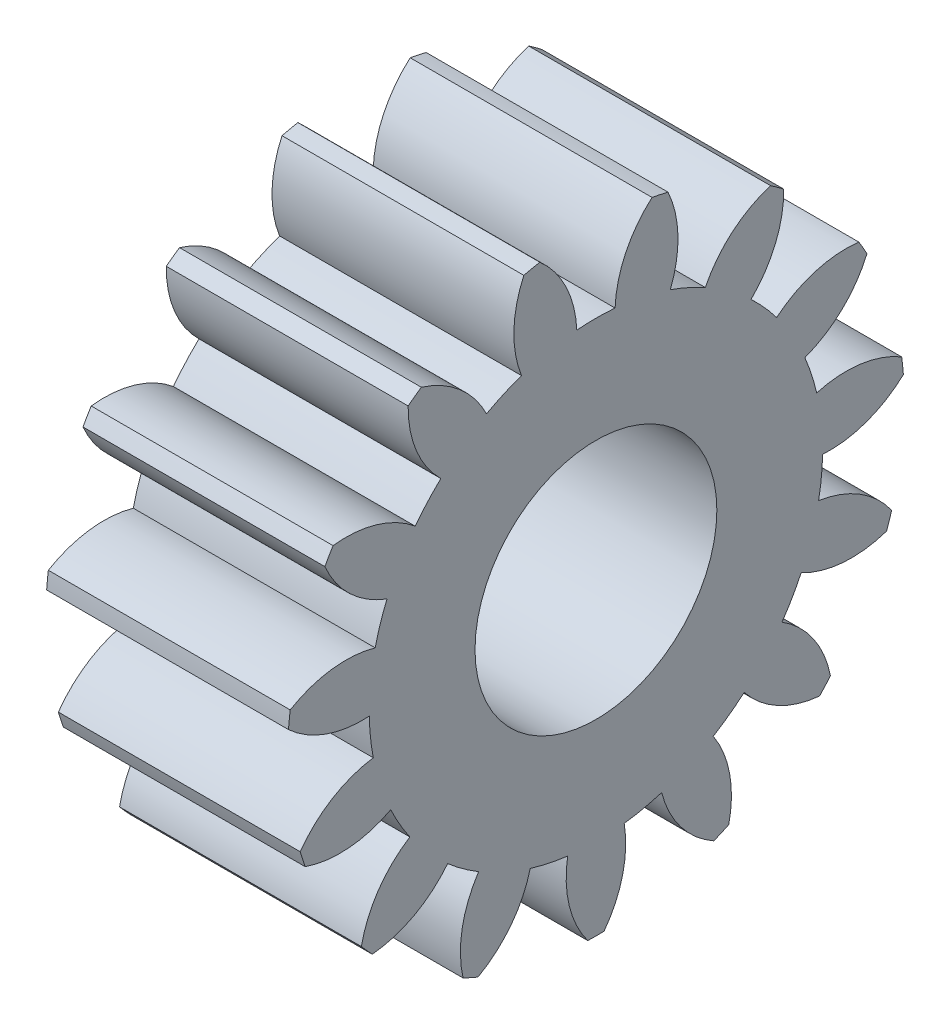
SolidWorks part; units mm, degrees
ref_plane "Plane1" through (0, 0, 0) normal (0, 0, 1) x (1, 0, 0)
ref_plane "Plane2" through (0, 0, 0) normal (0, 1, 0) x (1, 0, 0)
ref_plane "Plane3" through (0, 0, 0) normal (1, 0, 0) x (0, 0, -1)
other "Configuration Table"
sketch "HoldingSke" plane through (0, 0, 0) normal (0, 1, 0) x (1, 0, 0)
  line L0 (0, 0) -> (0.644, -0.1725)
  line L1 (-15, 0) -> (100, 0) construction
  line L2 (0, 0) -> (-2.1039, 2.3779)
  line L3 (0, 0) -> (-11.863, 4.5341)
  line L4 (0, 0) -> (8.3417, 2.2352)
  line L5 (0, 0) -> (-46.8476, -17.4728)
  line L6 (0, 0) -> (-8.2896, -5.593)
  line L7 (-2.1039, 2.3779) -> (8.6586, 51.2059)
  line L8 (-76.2, 54.61) -> (-74.4, 54.61)
  line L9 (-71.009, 38.7566) -> (-53.1078, 45.2721)
  line L10 (-76.2, 71.12) -> (104.1128, 71.12)
  line L11 (0, 0) -> (-10, 0)
  line L12 (-76.2, 101.6) -> (-76.147, 101.6)
  line L13 (24.9733, 27.94) -> (52.9518, 28.4284)
  line L14 (24.9733, 27.94) -> (24.9743, 27.94)
  line L15 (24.9733, 27.94) -> (100.4006, 29.5858)
  line L16 (-63.627, -1.5) -> (-12.827, -1.5)
  circle A0 centre (0, 0) radius 5
  circle A1 centre (0, 0) radius 9.374
  circle A2 centre (0, 0) radius 37.5
  circle A3 centre (0, 0) radius 5
  dimension "MHD" = 18.748
  dimension "Hub_dia" = 75
  dimension "Bore" = 10
  dimension "MBD" = 10
  dimension "Num_teeth" = 15
  dimension "Pitch" = 0.6667
  dimension "Overall_len" = 50
  dimension "Show_teeth" = 15
  dimension "Thickness" = 10
  dimension "OAL" = 50.0001
  dimension "T_dim" = 1.8
  dimension "Ap" = 20
  dimension "H" = 19.05
  dimension "Pitch_radius" = 180.3128
  dimension "Width" = 10
  dimension "Backlash" = 0.053
  dimension "Addendum_fac" = 1
  dimension "Dedendum_fac" = 1.25
  dimension "Clearance_fac" = 0.25
  dimension "Dedendum_add" = 0.001
  dimension "Module" = 1.5
sketch "BasProSke" plane through (0, 0, 0) normal (0, 1, 0) x (1, 0, 0)
  line L0 (-10, 0) -> (60, 0) construction
  line L1 (0, 0) -> (0, 12.75)
  line L2 (0, 0) -> (10, 0)
  line L3 (10, 0) -> (10, 12.75)
  line L4 (10, 12.75) -> (0, 12.75)
  dimension "Thickness" = 10
  dimension "Diameter" = 25.5
revolve "Base-Revolve" add sketch "BasProSke" angle 360 about L0
sketch "TooCutSke" plane through (0, 0, 0) normal (1, 0, 0) x (0, 0, -1)
  line L1 (0, 0) -> (0, 107) construction
  line L2 (0, 0) -> (-1.2686, 11.1782) construction
  line L3 (0, 0) -> (-4.6563, 21.9061) construction
  line L4 (-1.2686, 11.1782) -> (-2.3281, 10.953) construction
  arc A0 (0.7915, 9.3405) -> (-0.7915, 9.3405) centre (0, 0) ccw
  arc A1 (2.3447, 12.5584) -> (-2.3447, 12.5584) centre (0, 0) ccw
  circle A2 centre (0, 0) radius 11.25 construction
  circle A3 centre (0, 0) radius 10.5715 construction
  arc A4 (-0.7915, 9.3405) -> (-2.3447, 12.5584) centre (-5.2877, 9.1541) ccw
  arc A5 (2.3447, 12.5584) -> (0.7915, 9.3405) centre (5.2877, 9.1541) ccw
  dimension "Root_dia" = 18.748
  dimension "Overcut_dia" = 25.5508
  dimension "Pitch_dia" = 22.5
  dimension "Base_dia" = 21.1431
  dimension "Flank_rad" = 4.5
  dimension "Half_ang" = 12
  dimension "Half_CT" = 1.0832
extrude "ToothCut" cut sketch "TooCutSke" along normal through all
fillet "Breaks" [suppressed] radius 0.03
fillet "RootFillets" [suppressed] radius 0.376
pattern_circular "TeethCuts" count 15 every 24 about axis through (-10, 0, 0) along (1, 0, 0) of "ToothCut", "RootFillets", "Breaks"
sketch "HubNeaOneSke" plane through (0, 0, 0) normal (-1, 0, 0) x (0, 0, 1)
  circle A0 centre (0, 0) radius 9.374
  dimension "Diameter" = 18.748
extrude "HubNearOne" [suppressed] add sketch "HubNeaOneSke" along normal blind 40.0001
sketch "HubNeaBotSke" plane through (0, 0, 0) normal (-1, 0, 0) x (0, 0, 1)
  circle A0 centre (0, 0) radius 9.374
  dimension "Diameter" = 18.748
extrude "HubNearBoth" [suppressed] add sketch "HubNeaBotSke" along normal blind 20
ref_plane "FarPln" through (10, 0, 0) normal (1, 0, 0) x (0, 0, -1)
sketch "HubFarSke" plane through (10, 0, 0) normal (1, 0, 0) x (0, 0, -1)
  circle A0 centre (0, 0) radius 9.374
  dimension "Diameter" = 18.748
extrude "HubFar" [suppressed] add sketch "HubFarSke" along normal blind 20
sketch "BorSke" plane through (0, 0, 0) normal (1, 0, 0) x (0, 0, -1)
  circle A0 centre (0, 0) radius 5
  dimension "Diameter" = 10
extrude "Bore" cut sketch "BorSke" along normal mid plane 100.0001
sketch "KeySke" plane through (0, 0, 0) normal (1, 0, 0) x (0, 0, -1)
  line L0 (-2, 0) -> (-2, 6.8)
  line L1 (-2, 6.8) -> (2, 6.8)
  line L2 (2, 6.8) -> (2, 0)
  line L3 (0, 0) -> (0, 34) construction
  line L4 (-2, 0) -> (2, 0)
  dimension "Offset" = 6.8
  dimension "Width" = 4
extrude "Keyway" [suppressed] cut sketch "KeySke" along normal mid plane 100.0001
pattern_circular "Keyway2" [suppressed] count 2 every 90 about axis through (-10, 0, 0) along (1, 0, 0)
equation "' \"Module@HoldingSke\" = 6.35"
equation "' \"Num_teeth@HoldingSke\" = 12"
equation "' \"Ap@HoldingSke\" =  20"
equation "' \"Ap@HoldingSke\" = 20"
equation "' \"Width@HoldingSke\" = 0.5 * 25.4"
equation "' \"Hub_dia@HoldingSke\"= 1 * 25.4"
equation "' \"Hub_dia@HoldingSke\" = 1 * 25.4"
equation "' \"Overall_len@HoldingSke\" = 1.0 * 25.4"
equation "' \"Bore@HoldingSke\" = 0.75 * 25.4"
equation "' \"T_dim@HoldingSke\" = 0.1 * 25.4"
equation "' \"Width@KeySke\" = 0.25 * 25.4"
equation "' \"Show_teeth@HoldingSke\" = 13"
equation "' \"Backlash@HoldingSke\" = 0.009 * 25.4"
equation "' \"Addendum_fac@HoldingSke\" = 1.0"
equation "' \"Dedendum_fac@HoldingSke\" = 1.25"
equation "' \"Dedendum_add@HoldingSke\" = 0.00005 * 25.4"
equation "' \"Clearance_fac@HoldingSke\" = 0.25"
equation "\"Pitch@HoldingSke\" = 1 / \"Module@HoldingSke\""
equation "\"Overcut_dia@TooCutSke\" = (\"Num_teeth@HoldingSke\" + 2 * \"Addendum_fac@HoldingSke\") / \"Pitch@HoldingSke\" + 0.002 * 25.4"
equation "\"Pitch_dia@TooCutSke\" = \"Num_teeth@HoldingSke\" / \"Pitch@HoldingSke\""
equation "\"Base_dia@TooCutSke\" = \"Num_teeth@HoldingSke\" / \"Pitch@HoldingSke\" * cos((\"Ap@HoldingSke\"  * 3.14159265 / 180))"
equation "\"Root_dia@TooCutSke\" = (\"Num_teeth@HoldingSke\" + 2) / \"Pitch@HoldingSke\" - 2 * (\"Addendum_fac@HoldingSke\" + \"Dedendum_fac@HoldingSke\") / \"Pitch@HoldingSke\" - \"Dedendum_add@HoldingSke\" * 2"
equation "\"Half_ang@TooCutSke\" = 180 / \"Num_teeth@HoldingSke\""
equation "\"Half_CT@TooCutSke\" = \"Num_teeth@HoldingSke\" / \"Pitch@HoldingSke\" * sin((3.14159265 / 2 / \"Num_teeth@HoldingSke\")) / 2 - 7 * \"Backlash@HoldingSke\" / 4"
equation "\"Flank_rad@TooCutSke\" = \"Num_teeth@HoldingSke\" / \"Pitch@HoldingSke\" / 5"
equation "\"Radius@RootFillets\" = \"Clearance_fac@HoldingSke\" / \"Pitch@HoldingSke\" + \"Dedendum_add@HoldingSke\""
equation "\"Break_rad@Breaks\" = 0.02 / \"Pitch@HoldingSke\""
equation "\"Thickness@HoldingSke\" = \"Width@HoldingSke\""
equation "\"OAL@HoldingSke\" = \"Thickness@HoldingSke\""
equation "\"MHD@HoldingSke\" = (\"Num_teeth@HoldingSke\" + 2) / \"Pitch@HoldingSke\" - 2 * (\"Addendum_fac@HoldingSke\" + \"Dedendum_fac@HoldingSke\")  / \"Pitch@HoldingSke\" - \"Dedendum_add@HoldingSke\" * 2"
equation "\"MBD@HoldingSke\" = (\"Num_teeth@HoldingSke\" + 2) / \"Pitch@HoldingSke\" - 2 * (\"Addendum_fac@HoldingSke\" + \"Dedendum_fac@HoldingSke\")  / \"Pitch@HoldingSke\" - \"Dedendum_add@HoldingSke\" * 2 - 0.002 * 25.4"
equation "\"MHD@HoldingSke\" = ((sgn( \"MHD@HoldingSke\" - \"Hub_dia@HoldingSke\" )-1)*( \"MHD@HoldingSke\" - \"Hub_dia@HoldingSke\" ))/-2+ \"Hub_dia@HoldingSke\""
equation "\"MBD@HoldingSke\" = ((sgn( \"MBD@HoldingSke\" - \"Bore@HoldingSke\" )-1)*( \"MBD@HoldingSke\" - \"Bore@HoldingSke\" ))/-2+ \"Bore@HoldingSke\""
equation "\"OAL@HoldingSke\" = ((sgn( \"OAL@HoldingSke\" - \"Overall_len@HoldingSke\" )+1)*( \"OAL@HoldingSke\" - \"Overall_len@HoldingSke\" ))/2 + \"Overall_len@HoldingSke\" + 0.000002 * 25.4"
equation "\"Num_teeth@TeethCuts\" = int( \"Show_teeth@HoldingSke\" ) + 1"
equation "\"Num_teeth@TeethCuts\" = ((sgn( \"Num_teeth@TeethCuts\" - \"Num_teeth@HoldingSke\" )-1)*( \"Num_teeth@TeethCuts\" - \"Num_teeth@HoldingSke\" ))/-2+ \"Num_teeth@HoldingSke\""
equation "\"Num_teeth@TeethCuts\" = ((sgn( \"Num_teeth@TeethCuts\" - 2.0)+1)*( \"Num_teeth@TeethCuts\" - 2.0))/2 +2.0"
equation "\"Angle@TeethCuts\" = 360.0 / \"Num_teeth@HoldingSke\""
equation "\"Diameter@BasProSke\" = (\"Num_teeth@HoldingSke\" + 2 * \"Addendum_fac@HoldingSke\") / \"Pitch@HoldingSke\""
equation "\"Thickness@BasProSke\"  = \"Thickness@HoldingSke\""
equation "' \"Fillet_rad@BasProSke\" =  \"Thickness@HoldingSke\" * 0.05"
equation "' \"Fillet_rad@BasProSke\" = \"Thickness@HoldingSke\" * 0.05"
equation "\"MHD@HoldingSke\" = ((sgn( \"MHD@HoldingSke\" - \"Root_dia@TooCutSke\" )-1)*( \"MHD@HoldingSke\" - \"Root_dia@TooCutSke\" ))/-2+ \"Root_dia@TooCutSke\""
equation "\"Diameter@HubNeaOneSke\" = \"MHD@HoldingSke\""
equation "\"Length@HubNearOne\" = \"OAL@HoldingSke\" - \"Thickness@BasProSke\""
equation "\"Diameter@HubNeaBotSke\" = \"MHD@HoldingSke\""
equation "\"Length@HubNearBoth\" = ( \"OAL@HoldingSke\" - \"Thickness@BasProSke\" ) / 2.0"
equation "\"Thickness@FarPln\" = \"Thickness@BasProSke\""
equation "\"Diameter@HubFarSke\" = \"MHD@HoldingSke\""
equation "\"Length@HubFar\" = ( \"OAL@HoldingSke\" - \"Thickness@BasProSke\" ) / 2.0"
equation "\"Diameter@BorSke\" = \"MBD@HoldingSke\""
equation "\"D1@Bore\" = \"OAL@HoldingSke\" * 2.0"
equation "\"D1@Keyway\" = \"OAL@HoldingSke\" * 2.0"
equation "\"Offset@KeySke\" = \"T_dim@HoldingSke\" + \"MBD@HoldingSke\" / 2.0"
